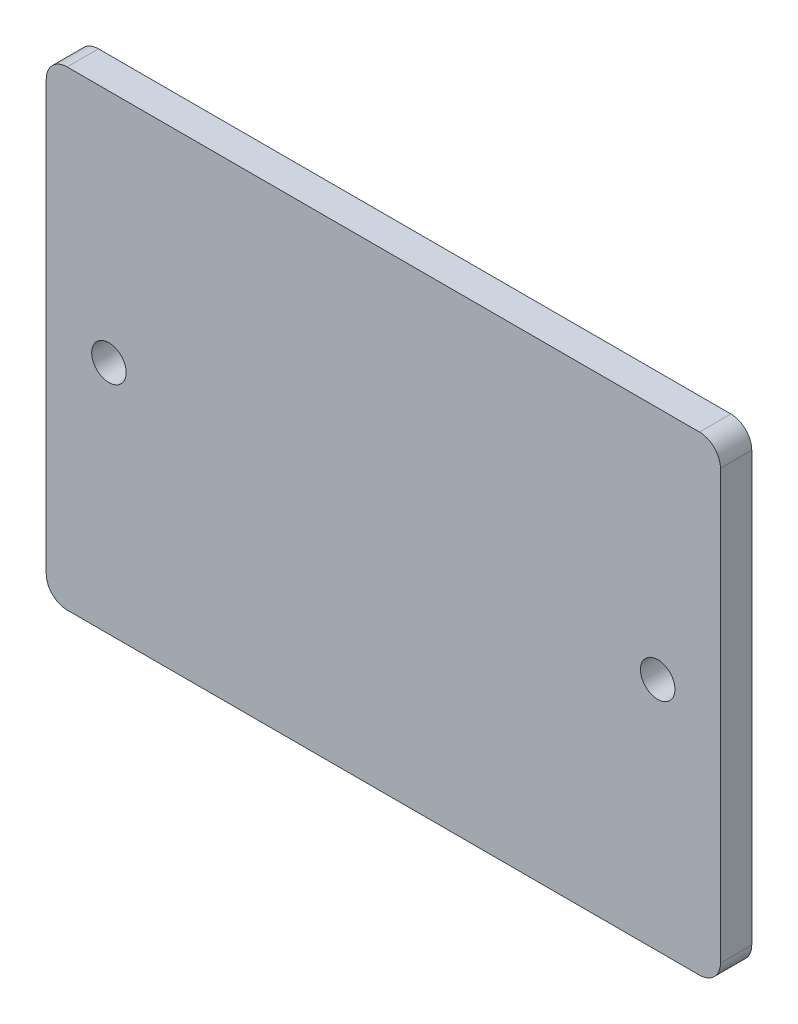
SolidWorks part; units mm, degrees
material "玻璃"
ref_plane "前视基准面" through (0, 0, 0) normal (0, 0, 1) x (1, 0, 0)
ref_plane "上视基准面" through (0, 0, 0) normal (0, 1, 0) x (1, 0, 0)
ref_plane "右视基准面" through (0, 0, 0) normal (1, 0, 0) x (0, 0, -1)
sketch "草图1" plane through (0, 0, 0) normal (0, 0, 1) x (1, 0, 0)
  line L1 (-32.25, -22.5) -> (32.25, -22.5)
  line L2 (-32.25, -22.5) -> (-32.25, 22.5)
  line L3 (-32.25, 22.5) -> (32.25, 22.5)
  line L4 (32.25, -22.5) -> (32.25, 22.5)
  line L5 (-32.25, -22.5) -> (32.25, 22.5) construction
  line L6 (-32.25, 22.5) -> (32.25, -22.5) construction
  point P0 (0, 0)
  dimension "D1" = 64.5
  dimension "D2" = 45
extrude "凸台-拉伸1" add sketch "草图1" along normal blind 3
sketch "草图6" plane through (0, 0, 3) normal (0, 0, 1) x (1, 0, 0)
  line L0 (32.25, -22.5) -> (32.25, 22.5) construction
  line L1 (26.25, -5) -> (38.25, -5)
  line L2 (26.25, -5) -> (26.25, 5)
  line L3 (26.25, 5) -> (38.25, 5)
  line L4 (38.25, -5) -> (38.25, 5)
  line L5 (26.25, -5) -> (38.25, 5) construction
  line L6 (26.25, 5) -> (38.25, -5) construction
  line L7 (0, 0) -> (0, 24.4085) construction
  line L8 (-26.25, 5) -> (-38.25, -5) construction
  line L9 (-26.25, -5) -> (-38.25, 5) construction
  line L10 (-38.25, -5) -> (-38.25, 5)
  line L11 (-26.25, 5) -> (-38.25, 5)
  line L12 (-26.25, -5) -> (-26.25, 5)
  line L13 (-26.25, -5) -> (-38.25, -5)
  point P0 (32.25, 0)
  point P14 (-32.25, 0)
  dimension "D1" = 6
  dimension "D2" = 10
extrude "凸台-拉伸4" add sketch "草图6" against normal up to surface (3 mm away) up to face at (0, 0, 0)
fillet "圆角1" radius 2 12 edges at (-32.25, 22.5, 1.5) (32.25, 22.5, 1.5) (32.25, 5, 1.5) (38.25, 5, 1.5) (38.25, -5, 1.5) (32.25, -5, 1.5) (32.25, -22.5, 1.5) (-32.25, -22.5, 1.5) (-38.25, -5, 1.5) (-38.25, 5, 1.5) (-32.25, -5, 1.5) (-32.25, 5, 1.5)
sketch "草图7" plane through (0, 0, 3) normal (0, 0, 1) x (1, 0, 0)
  line L0 (-35.25, 5) -> (-35.25, -5) construction
  line L1 (-34.25, 5) -> (-36.25, 5) construction
  line L2 (-36.25, -5) -> (-34.25, -5) construction
  line L3 (0, 0) -> (0, 44.1658) construction
  line L4 (35.25, 5) -> (35.25, -5) construction
  circle A0 centre (-35.25, 0) radius 1.65
  circle A1 centre (35.25, 0) radius 1.65
  dimension "D1" = 3.3
extrude "切除-拉伸3" cut sketch "草图7" against normal blind 6
sketch "草图8" plane through (0, 0, 3) normal (0, 0, 1) x (1, 0, 0)
  line L0 (-26.25, 0) -> (0, 0) construction
  line L2 (0, 0) -> (0, -34.1184) construction
  circle A0 centre (-26.25, 0) radius 1.65
  circle A1 centre (-35.25, 0) radius 1.65 construction
  circle A3 centre (26.25, 0) radius 1.65
  dimension "D1" = 26.25
sketch "草图9" plane through (0, 0, 3) normal (0, 0, 1) x (1, 0, 0)
  line L0 (-38.25, 3) -> (-38.25, -3) construction
  line L1 (-32.25, 7) -> (-38.25, 7)
  line L2 (-32.25, 7) -> (-32.25, -7)
  line L3 (-32.25, -7) -> (-38.25, -7)
  line L4 (-38.25, 7) -> (-38.25, -7)
  line L5 (0, 0) -> (0, 36.3262) construction
  line L6 (38.25, 7) -> (38.25, -7)
  line L7 (32.25, -7) -> (38.25, -7)
  line L8 (32.25, 7) -> (32.25, -7)
  line L9 (32.25, 7) -> (38.25, 7)
extrude "切除-拉伸4" cut sketch "草图9" against normal blind 10
extrude "切除-拉伸5" cut sketch "草图8" against normal blind 10
sketch "草图10" plane through (0, 0, 3) normal (0, 0, 1) x (1, 0, 0)
  line L0 (0, 0) -> (0, -17) construction
  line L2 (-1.05, -12) -> (1.05, -12)
  line L3 (-1.05, -12) -> (-1.05, -22)
  line L4 (-1.05, -22) -> (1.05, -22)
  line L5 (1.05, -12) -> (1.05, -22)
  line L6 (-1.05, -12) -> (1.05, -22) construction
  line L7 (-1.05, -22) -> (1.05, -12) construction
  dimension "D1" = 2.1
  dimension "D2" = 10
  dimension "D3" = 17
extrude "切除-拉伸6" [suppressed] cut sketch "草图10" against normal blind 10
fillet "圆角2" [suppressed] radius 1
